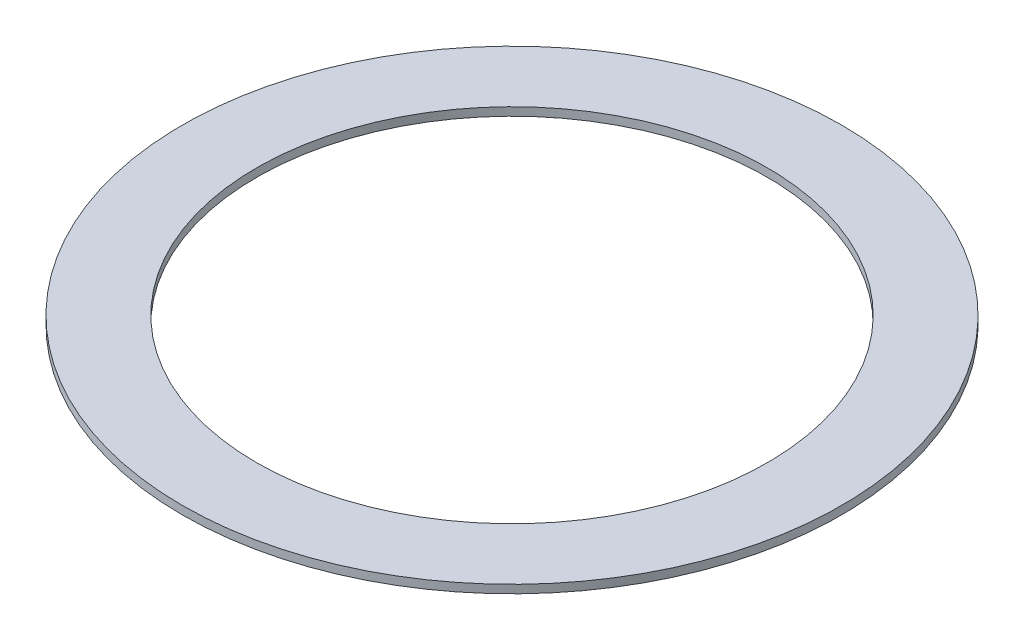
SolidWorks part; units mm, degrees
ref_plane "Front" through (0, 0, 0) normal (0, 0, 1) x (1, 0, 0)
ref_plane "Top" through (0, 0, 0) normal (0, 1, 0) x (1, 0, 0)
ref_plane "Right" through (0, 0, 0) normal (1, 0, 0) x (0, 0, -1)
sketch "Esquisse1" plane through (0, 0, 0) normal (0, 1, 0) x (1, 0, 0)
  circle A0 centre (0, 0) radius 1.55
  circle A1 centre (0, 0) radius 2
  dimension "D1" = 3.1
  dimension "D2" = 4
extrude "Boss.-Extru.1" add sketch "Esquisse1" along normal blind 0.05
scale "Echelle1" scale about origin uniform scaling yes scale factor 10
